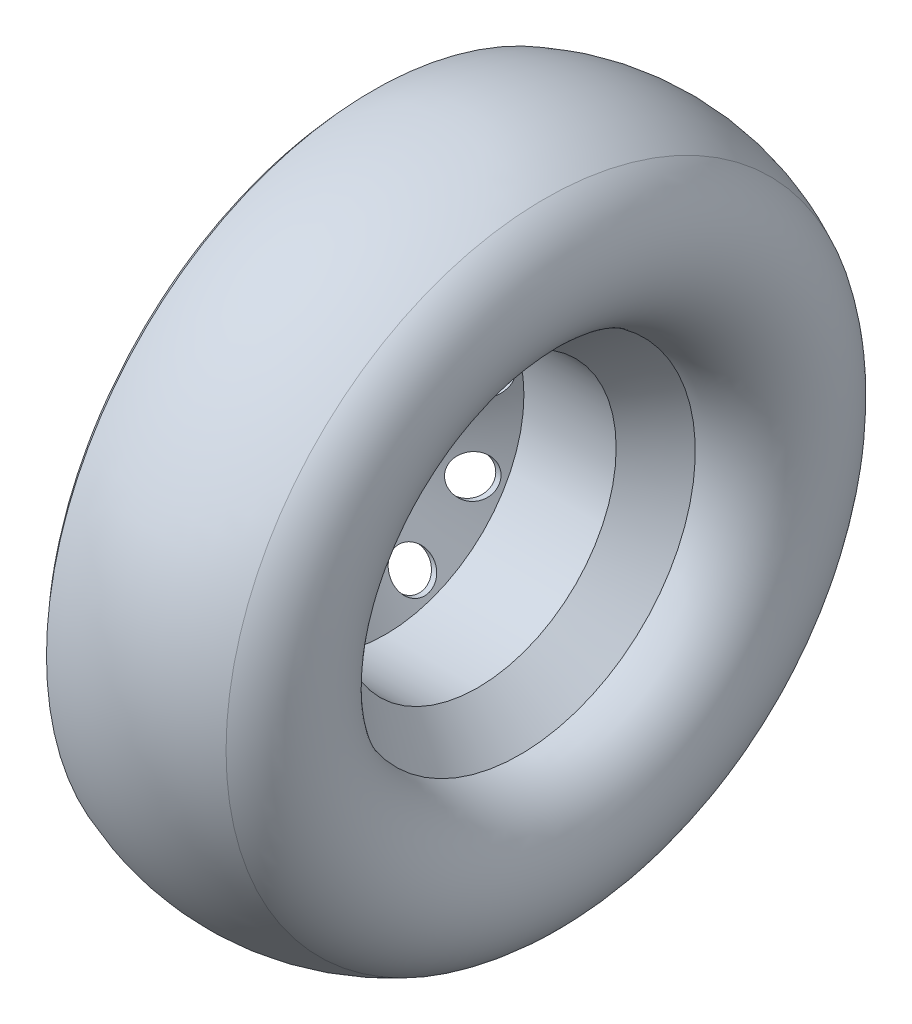
SolidWorks part; units mm, degrees
ref_plane "Front Plane" through (0, 0, 0) normal (0, 0, 1) x (1, 0, 0)
ref_plane "Top Plane" through (0, 0, 0) normal (0, 1, 0) x (1, 0, 0)
ref_plane "Right Plane" through (0, 0, 0) normal (1, 0, 0) x (0, 0, -1)
sketch "Sketch1" plane through (0, 0, 0) normal (0, 0, 1) x (1, 0, 0)
  line L0 (35, 140) -> (0, 80)
  line L2 (5, 80) -> (35, 131.4286)
  line L3 (35, 140) -> (26.6394, 160)
  line L4 (26.6394, 160) -> (26.6394, 200)
  line L5 (35, 131.4286) -> (122.588, 131.4286)
  line L6 (122.588, 131.4286) -> (162.588, 166.5636)
  line L7 (0, 0) -> (270.4402, 0) construction
  line L8 (0, 80) -> (0, 50)
  line L9 (0, 50) -> (5, 50)
  line L10 (5, 50) -> (5, 80)
  arc A0 (26.6394, 200) -> (23.024, 310) centre (75.7623, 256.674) cw
  arc A1 (162.588, 166.5636) -> (186.147, 302.5951) centre (145.4702, 239.584) ccw
  arc A2 (23.024, 310) -> (186.147, 302.5951) centre (96.3061, 123.9094) cw
  point P14 (164.7548, 167.1057)
  dimension "D10" = 75
  dimension "D12" = 200
  dimension "D1" = 80
  dimension "D2" = 5
  dimension "D3" = 60
  dimension "D4" = 30
  dimension "D5" = 20
  dimension "D6" = 40
  dimension "D7" = 30
  dimension "D8" = 140
  dimension "D9" = 40
  dimension "D11" = 230
  dimension "D13" = 30
revolve "Revolve4" add sketch "Sketch1" angle 360 about L7
sketch "Sketch2" plane through (0, 0, 0) normal (-1, 0, 0) x (0, 0, 1)
  circle A0 centre (0, 60) radius 7.5
  circle A1 centre (0, 110) radius 17.5
  circle A2 centre (70.7066, 84.2649) radius 17.5
  circle A3 centre (108.3289, 19.1013) radius 17.5
  circle A4 centre (95.2628, -55) radius 17.5
  circle A5 centre (37.6222, -103.3662) radius 17.5
  circle A6 centre (-37.6222, -103.3662) radius 17.5
  circle A7 centre (-95.2628, -55) radius 17.5
  circle A8 centre (-108.3289, 19.1013) radius 17.5
  circle A9 centre (-70.7066, 84.2649) radius 17.5
  circle A10 centre (46.9099, 37.4094) radius 7.5
  circle A11 centre (58.4957, -13.3513) radius 7.5
  circle A12 centre (26.033, -54.0581) radius 7.5
  circle A13 centre (-26.033, -54.0581) radius 7.5
  circle A14 centre (-58.4957, -13.3513) radius 7.5
  circle A15 centre (-46.9099, 37.4094) radius 7.5
  point P23 (0, 0)
  point P36 (0, 0)
  dimension "D3" = 35
  dimension "D4" = 15
  dimension "D1" = 60
  dimension "D2" = 110
  dimension "D5" = 9
  dimension "D6" = 7
extrude "Cut-Extrude1" cut sketch "Sketch2" against normal through all
ref_plane "Plane1" through (0, 340, 0) normal (0, 1, 0) x (1, 0, 0)
sketch "Sketch3" plane through (0, 340, 0) normal (0, 1, 0) x (1, 0, 0)
  line L0 (23.024, 189.5305) -> (43.024, 213.5269)
  line L1 (23.024, -310) -> (23.024, 310) construction
  line L2 (43.024, 213.5269) -> (59.915, 189.5305)
  line L3 (59.915, 189.5305) -> (77.6578, 210.8187)
  line L4 (77.6578, 210.8187) -> (81.9832, 189.5305)
  line L5 (81.9832, 189.5305) -> (97.6211, 208.2931)
  line L6 (97.6211, 208.2931) -> (110.828, 189.5305)
  line L7 (110.828, 189.5305) -> (125.2571, 206.8428)
  line L8 (125.2571, 206.8428) -> (137.4431, 189.5305)
  line L9 (137.4431, 189.5305) -> (149.833, 205.714)
  line L10 (149.833, 205.714) -> (161.2245, 189.5305)
  line L11 (161.2245, 189.5305) -> (173.3518, 205.3711)
  line L12 (173.3518, 205.3711) -> (184.502, 189.5305)
  line L13 (184.502, 189.5305) -> (186.147, 211.4251)
  line L14 (186.147, -302.5951) -> (186.147, 302.5951) construction
  line L16 (186.147, 227.9389) -> (177.1694, 218.9612)
  line L17 (177.1694, 218.9612) -> (164.5114, 231.6193)
  line L18 (164.5114, 231.6193) -> (155.2079, 220.0815)
  line L19 (155.2079, 220.0815) -> (140.8993, 231.6193)
  line L20 (140.8993, 231.6193) -> (131.6039, 220.0914)
  line L21 (131.6039, 220.0914) -> (117.3075, 231.6193)
  line L22 (117.3075, 231.6193) -> (107.6471, 219.6388)
  line L23 (107.6471, 219.6388) -> (95.6666, 231.6193)
  line L24 (95.6666, 231.6193) -> (86.4258, 220.1592)
  line L25 (86.4258, 220.1592) -> (74.9658, 231.6193)
  line L26 (74.9658, 231.6193) -> (60.0393, 216.6928)
  line L27 (60.0393, 216.6928) -> (45.1128, 231.6193)
  line L28 (45.1128, 231.6193) -> (23.024, 209.5305)
  line L29 (23.024, 209.5305) -> (23.024, 189.5305)
  line L30 (186.147, 211.4251) -> (186.147, 227.9389)
  point P29 (0, 0)
  point P33 (0, 0)
  dimension "D1" = 20
  dimension "D2" = 20
